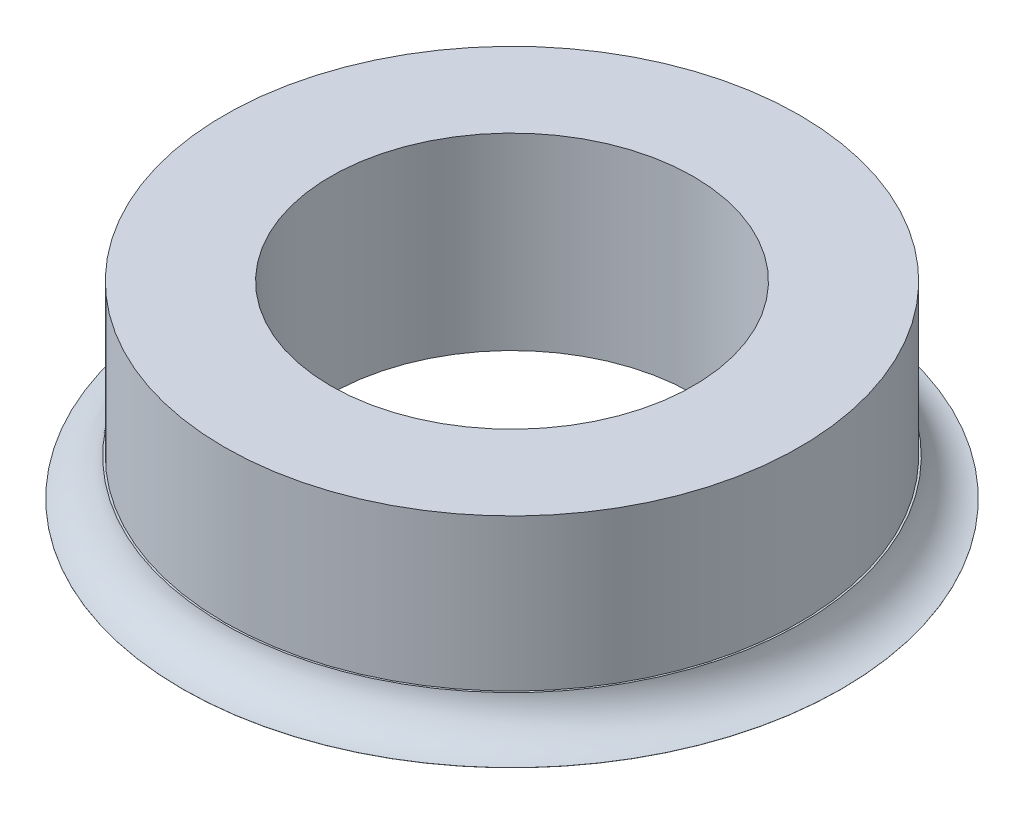
SolidWorks part; units mm, degrees
material "Полиамид ПА-6Б ТУ 6-05-988-93"
ref_plane "Спереди" through (0, 0, 0) normal (0, 0, 1) x (1, 0, 0)
ref_plane "Сверху" through (0, 0, 0) normal (0, 1, 0) x (1, 0, 0)
ref_plane "Справа" through (0, 0, 0) normal (1, 0, 0) x (0, 0, -1)
sketch "Эскиз1" plane through (0, 0, 0) normal (0, 1, 0) x (1, 0, 0)
  circle A0 centre (0, 0) radius 2.475
  circle A1 centre (0, 0) radius 3.925
  dimension "D1" = 4.95
  dimension "D2" = 7.85
extrude "Бобышка-Вытянуть1" add sketch "Эскиз1" along normal blind 2.57
sketch "Эскиз2" plane through (0, 0, 0) normal (0, -1, 0) x (1, 0, 0)
  circle A0 centre (0, 0) radius 4.5
  circle A1 centre (0, 0) radius 3.925 construction
  circle A2 centre (0, 0) radius 3.925
  dimension "D1" = 9
extrude "Бобышка-Вытянуть2" add sketch "Эскиз2" against normal blind 0.5
sketch "Эскиз3" plane through (0, 0, 0) normal (0, 0, 1) x (1, 0, 0)
  line L0 (4.5, 0.5) -> (-4.5, 0.5) construction
  line L1 (-4.5, 0.5) -> (-4.5, 0) construction
  line L2 (-3.925, 2.57) -> (-3.925, 0.5) construction
  line L3 (-4.5, 0) -> (4.5, 0) construction
  line L4 (-4.5, 0.0014) -> (-4.5, 0.5)
  line L5 (-4.5, 0.5) -> (-3.95, 0.5)
  line L6 (0, 0) -> (0, 2.57) construction
  line L7 (2.475, 2.57) -> (-2.475, 2.57) construction
  arc A0 (-3.95, 0.5) -> (-4.5, 0.0014) centre (-4.5416, 0.6) cw
  dimension "D1" = 0.6
  dimension "D2" = 0.025
revolve "Вырез-Повернуть1" cut sketch "Эскиз3" angle 360 about L6
